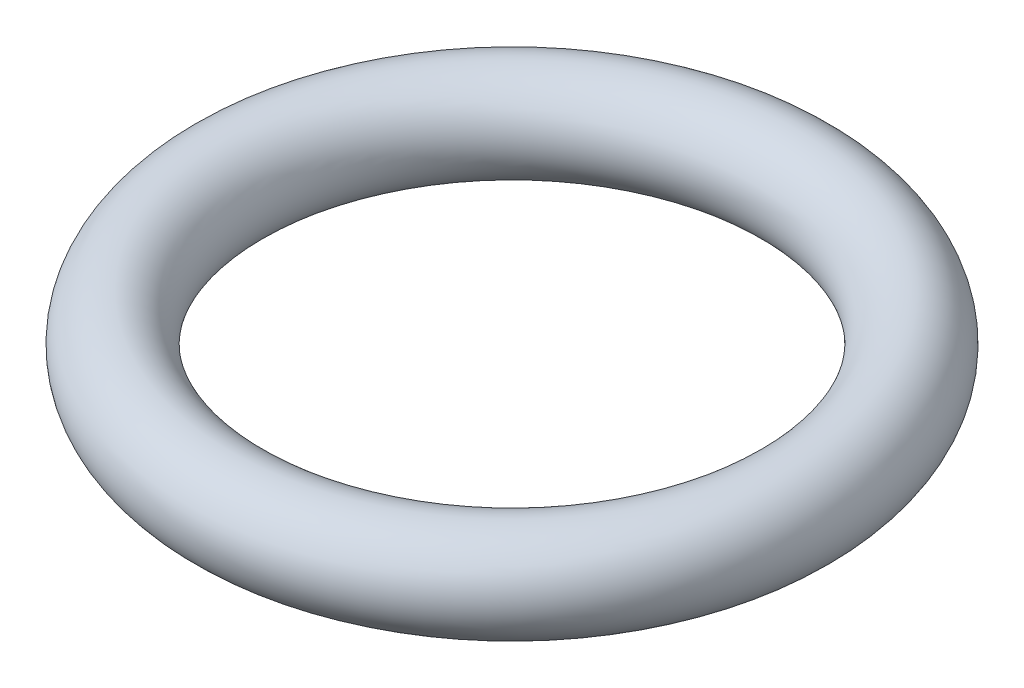
SolidWorks part; units mm, degrees
ref_plane "Front Plane" through (0, 0, 0) normal (0, 0, 1) x (1, 0, 0)
ref_plane "Top Plane" through (0, 0, 0) normal (0, 1, 0) x (1, 0, 0)
ref_plane "Right Plane" through (0, 0, 0) normal (1, 0, 0) x (0, 0, -1)
sketch "Sketch1" plane through (0, 0, 0) normal (0, 1, 0) x (1, 0, 0)
  circle A0 centre (0, 0) radius 152.4
  dimension "D1" = 304.8
sketch "Sketch2" plane through (0, 0, 0) normal (0, 0, 1) x (1, 0, 0)
  circle A0 centre (-152.4, 0) radius 25.4
  dimension "D1" = 50.8
sweep "Sweep1" add profiles "Sketch2" path "Sketch1"
